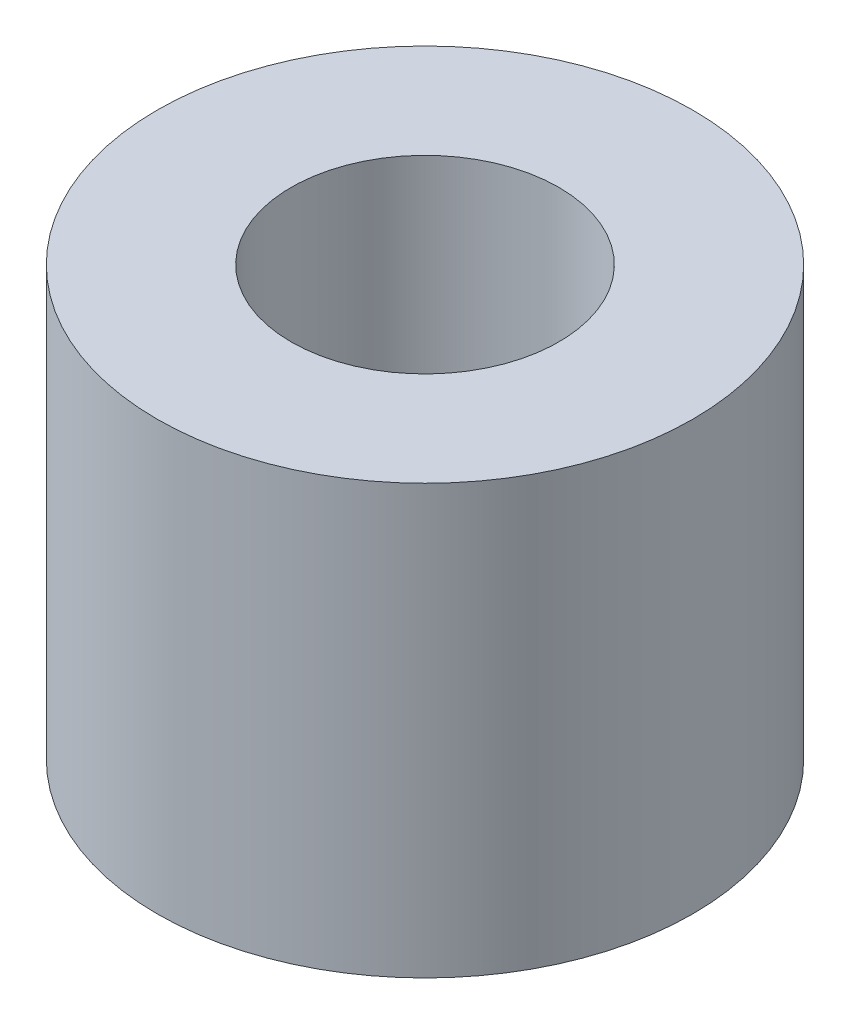
SolidWorks part; units mm, degrees
material "Acrylic (Medium-high impact)"
ref_plane "Front Plane" through (0, 0, 0) normal (0, 0, 1) x (1, 0, 0)
ref_plane "Top Plane" through (0, 0, 0) normal (0, 1, 0) x (1, 0, 0)
ref_plane "Right Plane" through (0, 0, 0) normal (1, 0, 0) x (0, 0, -1)
sketch "Sketch1" plane through (0, 0, 0) normal (0, 1, 0) x (1, 0, 0)
  circle A0 centre (0, 0) radius 7.9375
  dimension "D1" = 15.875
extrude "Boss-Extrude1" add sketch "Sketch1" along normal blind 12.7
hole_wizard "3/8-16 Tapped Hole1" positions "Sketch3" profile "Sketch2" tap size "3/8-16" standard "Ansi Inch"
sketch "Sketch3" plane through (0, 12.7, 0) normal (0, 1, 0) x (-1, 0, 0)
  point P0 (0, 0)
sketch "Sketch2" plane through (0, 12.7, 0) normal (1, 0, 0) x (0, 0, 1)
  line L0 (0, 0) -> (0, 11.176)
  line L1 (0, 11.176) -> (3.9687, 11.176)
  line L2 (3.9687, 11.176) -> (3.9688, 0)
  line L5 (3.9688, 0) -> (0, 0)
  line L10 (0, 11.176) -> (-3.9688, 11.176) construction
  line L11 (0, -6.35) -> (0, 107.95) construction
  dimension "Tap Drill Dia." = 7.9375
  dimension "Tap Drill Depth" = 11.176
  dimension "Drill Angle" = 180
cosmetic thread "Hole Thread1" parameters "D1"=11.176, "D2"=9.525
